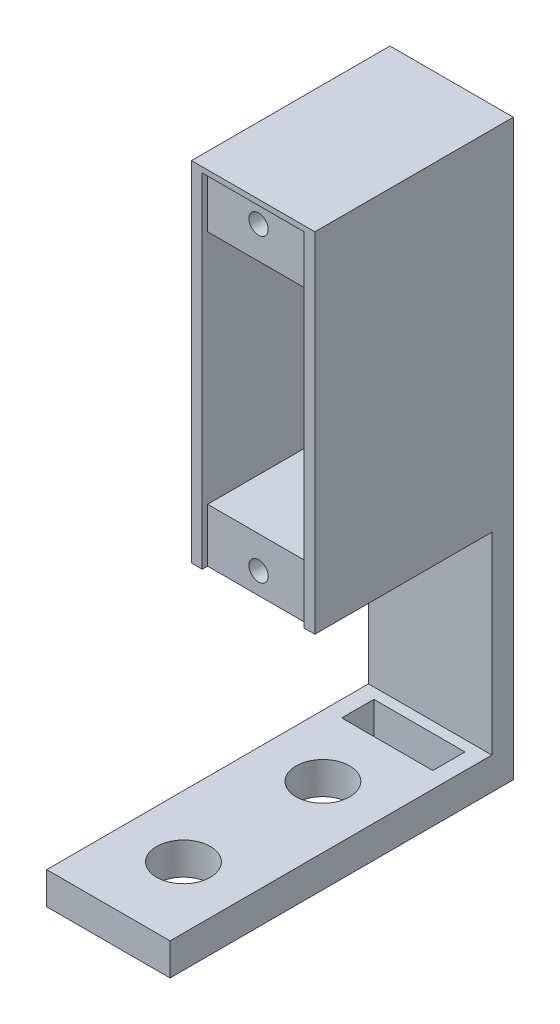
SolidWorks part; units mm, degrees
ref_plane "Plan de face" through (0, 0, 0) normal (0, 0, 1) x (1, 0, 0)
ref_plane "Plan de dessus" through (0, 0, 0) normal (0, 1, 0) x (1, 0, 0)
ref_plane "Plan de droite" through (0, 0, 0) normal (1, 0, 0) x (0, 0, -1)
sketch "Esquisse1" plane through (0, 0, 0) normal (0, 0, 1) x (1, 0, 0)
  line L1 (0, 0) -> (-11.5, 0)
  line L2 (0, 0) -> (0, 32.5)
  line L3 (0, 32.5) -> (-11.5, 32.5)
  line L4 (-11.5, 0) -> (-11.5, 32.5)
  dimension "D1" = 11.5
  dimension "D2" = 32.5
extrude "Boss.-Extru.1" add sketch "Esquisse1" along normal blind 18.5
sketch "Esquisse4" plane through (0, 0, 18.5) normal (0, 0, 1) x (1, 0, 0)
  line L0 (0, 32.5) -> (-11.5, 32.5) construction
  line L1 (-10.5, 32) -> (-1, 32)
  line L2 (-10.5, 32) -> (-10.5, 0)
  line L3 (-10.5, 0) -> (-1, 0)
  line L4 (-1, 32) -> (-1, 0)
  line L5 (-11.5, 0) -> (0, 0) construction
  line L6 (0, 0) -> (0, 32.5) construction
  line L7 (-11.5, 32.5) -> (-11.5, 0) construction
  dimension "D1" = 0.5
  dimension "D2" = 0
  dimension "D3" = 1
  dimension "D4" = 1
extrude "Enlèv. mat.-Extru.1" cut sketch "Esquisse4" against normal blind 16.5
sketch "Esquisse5" plane through (0, 0, 2) normal (0, 0, 1) x (1, 0, 0)
  line L0 (-1, 0) -> (-1, 32) construction
  line L1 (-10.5, 32) -> (-1, 32)
  line L2 (-10.5, 32) -> (-10.5, 27)
  line L3 (-10.5, 27) -> (-1, 27)
  line L4 (-1, 32) -> (-1, 27)
  line L5 (0, 32.5) -> (-11.5, 32.5) construction
  dimension "D1" = 0.5
  dimension "D2" = 5
extrude "Boss.-Extru.2" add sketch "Esquisse5" along normal blind 16
sketch "Esquisse6" plane through (0, 0, 18) normal (0, 0, 1) x (1, 0, 0)
  line L0 (-10.5, 32) -> (-10.5, 0) construction
  line L4 (-10.5, 27) -> (-1, 27) construction
  circle A0 centre (-5.75, 30) radius 0.9
  point P4 (0, 0)
  point P5 (0, 0)
  point P8 (0, 0)
  dimension "D2" = 1.8
  dimension "D1" = 4.75
  dimension "D3" = 3
extrude "Enlèv. mat.-Extru.2" cut sketch "Esquisse6" against normal blind 6
sketch "Esquisse7" plane through (0, 0, 0) normal (0, -1, 0) x (1, 0, 0)
  line L0 (-11.5, 18.5) -> (-11.5, 0) construction
  line L1 (0, 0) -> (-11.5, 0)
  line L2 (0, 0) -> (0, 2)
  line L3 (0, 2) -> (-11.5, 2)
  line L4 (-11.5, 0) -> (-11.5, 2)
  dimension "D1" = 11.5
  dimension "D2" = 2
extrude "Boss.-Extru.3" add sketch "Esquisse7" along normal blind 21
sketch "Esquisse8" plane through (0, 0, 18) normal (0, 0, 1) x (1, 0, 0)
  line L0 (-5.75, 32) -> (-5.75, -3.1181) construction
  line L1 (-1, 32) -> (-10.5, 32) construction
  line L2 (-10.5, 0) -> (-1, 0) construction
  line L3 (-1, 0) -> (-1, 16) construction
  line L4 (-1, 0) -> (-1, 32) construction
  line L5 (-1, 16) -> (-10.5, 16) construction
  line L6 (-10.5, 32) -> (-10.5, 0) construction
sketch "Esquisse9" plane through (0, 0, 2) normal (0, 0, 1) x (1, 0, 0)
  line L0 (-11.5, 0) -> (0, 0) construction
  line L1 (0, 0) -> (0, 16.25) construction
  line L2 (0, 0) -> (0, 32.5) construction
  line L3 (0, 16.25) -> (-11.5, 16.25) construction
  line L4 (-11.5, 32.5) -> (-11.5, 0) construction
  line L5 (-10.5, 27) -> (-10.5, 0) construction
  line L6 (-1, 0) -> (-10.5, 0)
  line L7 (-1, 0) -> (-1, 5)
  line L8 (-1, 5) -> (-10.5, 5)
  line L9 (-10.5, 0) -> (-10.5, 5)
  dimension "D1" = 5
extrude "Boss.-Extru.4" add sketch "Esquisse9" along normal blind 16
sketch "Esquisse10" plane through (0, 0, 18) normal (0, 0, 1) x (1, 0, 0)
  line L0 (-5.75, 32) -> (-5.75, -3.1181) construction
  line L1 (-1, 5) -> (-10.5, 5) construction
  circle A1 centre (-5.75, 2) radius 0.9
  dimension "D1" = 1.8
  dimension "D2" = 1.8
  dimension "D3" = 3
extrude "Enlèv. mat.-Extru.3" cut sketch "Esquisse10" against normal blind 7
sketch "Esquisse11" plane through (0, 0, 0) normal (0, -1, 0) x (1, 0, 0)
  line L0 (-10.5, 18) -> (-10.5, 2) construction
  line L1 (0, 2) -> (-11.5, 2) construction
  line L2 (-1, 18) -> (-1, 2) construction
  line L4 (0, 2) -> (-11.5, 2) construction
  line L5 (0, 18.5) -> (0, 2) construction
  line L6 (-10.5, 9) -> (-1, 9)
  line L7 (-10.5, 9) -> (-10.5, 2)
  line L8 (-10.5, 2) -> (-1, 2)
  line L9 (-1, 9) -> (-1, 2)
  line L10 (-11.5, 18.5) -> (-11.5, 2) construction
  dimension "D1" = 0
  dimension "D2" = 7
  dimension "D3" = 7
  dimension "D4" = 1
  dimension "D5" = 1
extrude "Enlèv. mat.-Extru.4" cut sketch "Esquisse11" against normal blind 7
sketch "Esquisse12" plane through (0, 0, 2) normal (0, 0, 1) x (1, 0, 0)
  line L0 (-11.5, -21) -> (-11.5, 0) construction
  line L1 (0, -21) -> (-11.5, -21)
  line L2 (0, -21) -> (0, -18)
  line L3 (0, -18) -> (-11.5, -18)
  line L4 (-11.5, -21) -> (-11.5, -18)
  dimension "D1" = 3
  dimension "D2" = 11.5
extrude "Boss.-Extru.5" add sketch "Esquisse12" along normal blind 30
sketch "Esquisse13" plane through (0, -21, 0) normal (0, -1, 0) x (1, 0, 0)
  line L0 (0, 2) -> (-11.5, 2) construction
  line L1 (-11.5, 32) -> (0, 32) construction
  line L2 (-11.5, 32) -> (-11.5, 0) construction
  line L3 (0, 0) -> (0, 32) construction
  circle A0 centre (-5.75, 12) radius 2.5
  circle A1 centre (-5.75, 25) radius 2.5
  dimension "D1" = 5
  dimension "D2" = 7
  dimension "D3" = 5
  dimension "D4" = 13
  dimension "D5" = 5.75
  dimension "D6" = 5.75
extrude "Enlèv. mat.-Extru.5" cut sketch "Esquisse13" against normal blind 10
sketch "Esquisse15" plane through (0, -21, 0) normal (0, -1, 0) x (1, 0, 0)
  line L0 (4.2982, 2) -> (-15.3351, 2) construction
  line L1 (0, 0) -> (0, 32) construction
  line L2 (-10, 6) -> (-1.5, 6)
  line L3 (-10, 6) -> (-10, 3)
  line L4 (-10, 3) -> (-1.5, 3)
  line L5 (-1.5, 6) -> (-1.5, 3)
  line L7 (-11.5, 32) -> (-11.5, 0) construction
  point P7 (-1.5, 4.5)
  dimension "D1" = 1.5
  dimension "D2" = 1.5
  dimension "D3" = 3
  dimension "D4" = 1
extrude "Enlèv. mat.-Extru.6" cut sketch "Esquisse15" against normal blind 10
